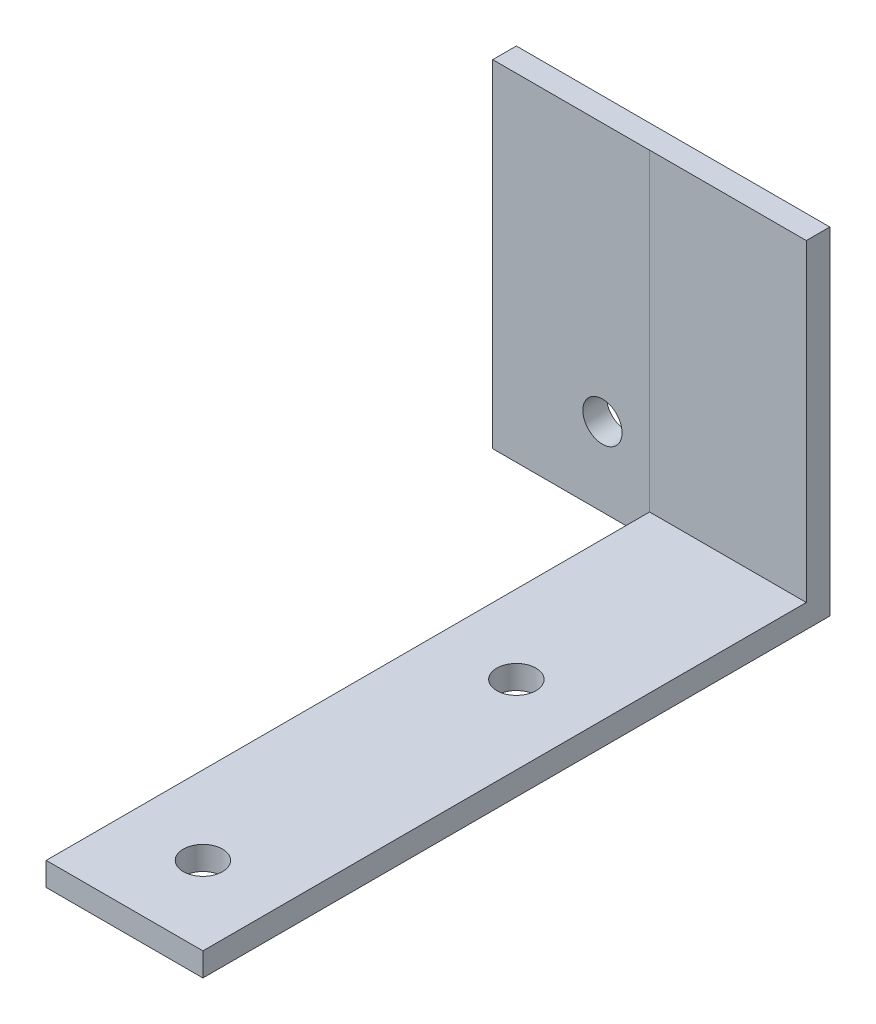
SolidWorks part; units mm, degrees
material "ABS"
ref_plane "Front Plane" through (0, 0, 0) normal (0, 0, 1) x (1, 0, 0)
ref_plane "Top Plane" through (0, 0, 0) normal (0, 1, 0) x (1, 0, 0)
ref_plane "Right Plane" through (0, 0, 0) normal (1, 0, 0) x (0, 0, -1)
sketch "Sketch1" plane through (0, 0, 0) normal (0, 1, 0) x (1, 0, 0)
  line L0 (0, 40) -> (0, -40) construction
  line L1 (-10, 40) -> (10, 40)
  line L2 (-10, 40) -> (-10, -40)
  line L3 (-10, -40) -> (10, -40)
  line L4 (10, 40) -> (10, -40)
  line L5 (-10, 40) -> (10, -40) construction
  line L6 (-10, -40) -> (10, 40) construction
  circle A1 centre (0, -30) radius 2.5
  circle A2 centre (0, 10) radius 2.5
  point P0 (0, 0)
  point P8 (0, -30.4782)
  point P9 (0, 9.784)
  point P14 (0, 0)
  point P15 (0, 12.7506)
extrude "Boss-Extrude1" add sketch "Sketch1" along normal blind 3
sketch "Sketch2" plane through (0, 3, 0) normal (0, 1, 0) x (1, 0, 0)
  line L0 (10, -40) -> (10, 40) construction
  line L1 (-10, 40) -> (10, 40)
  line L2 (-10, 40) -> (-10, 37)
  line L3 (-10, 37) -> (10, 37)
  line L4 (10, 40) -> (10, 37)
extrude "Boss-Extrude2" add sketch "Sketch2" along normal blind 40
sketch "Sketch4" plane through (-10, 0, 0) normal (-1, 0, 0) x (0, 0, 1)
  line L0 (-40, 0) -> (40, 0) construction
  line L1 (-40, 43) -> (-36.9847, 43)
  line L2 (-40, 43) -> (-40, 0)
  line L3 (-40, 0) -> (-36.9847, 0)
  line L4 (-36.9847, 43) -> (-36.9847, 0)
extrude "Boss-Extrude4" add sketch "Sketch4" along normal blind 20
sketch "Sketch7" plane through (0, 0, -40) normal (0, 0, -1) x (-1, 0, 0)
  line L0 (0, 0) -> (0, 43) construction
  line L1 (-10, 43) -> (30, 43) construction
  circle A0 centre (16, 10) radius 2.5
  point P8 (0, 10)
  point P9 (0, 10)
extrude "Cut-Extrude2" cut sketch "Sketch7" against normal blind 20
